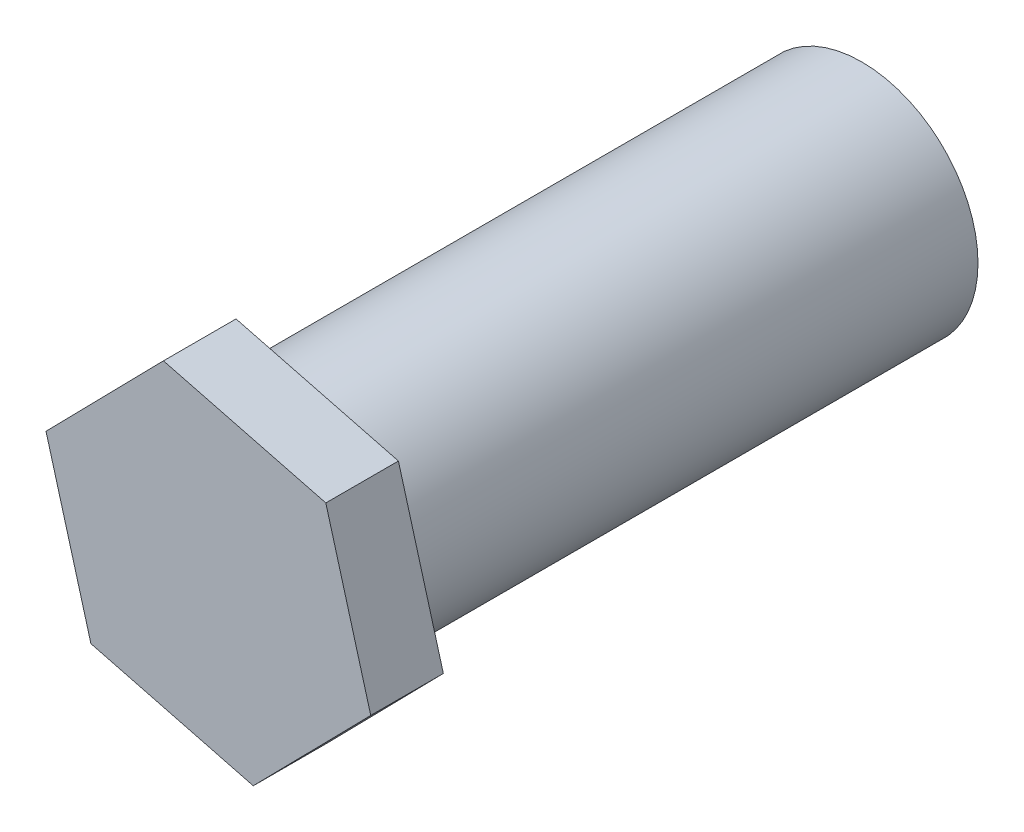
SolidWorks part; units mm, degrees
ref_plane "Plan de face" through (0, 0, 0) normal (0, 0, 1) x (1, 0, 0)
ref_plane "Plan de dessus" through (0, 0, 0) normal (0, 1, 0) x (1, 0, 0)
ref_plane "Plan de droite" through (0, 0, 0) normal (1, 0, 0) x (0, 0, -1)
sketch "Esquisse1" plane through (0, 0, 0) normal (0, 0, 1) x (1, 0, 0)
  circle A0 centre (0, 0) radius 40
  dimension "D1" = 80
extrude "Boss.-Extru.1" add sketch "Esquisse1" along normal blind 200
sketch "Esquisse2" plane through (0, 0, 200) normal (0, 0, 1) x (1, 0, 0)
  line L1 (55.9062, -14.4164) -> (40.438, 41.208)
  line L2 (40.438, 41.208) -> (-15.4682, 55.6244)
  line L3 (-15.4682, 55.6244) -> (-55.9062, 14.4164)
  line L4 (-55.9062, 14.4164) -> (-40.438, -41.208)
  line L5 (-40.438, -41.208) -> (15.4682, -55.6244)
  line L6 (15.4682, -55.6244) -> (55.9062, -14.4164)
  circle A0 centre (0, 0) radius 50 construction
  dimension "D1" = 100
extrude "Boss.-Extru.2" add sketch "Esquisse2" along normal blind 25
